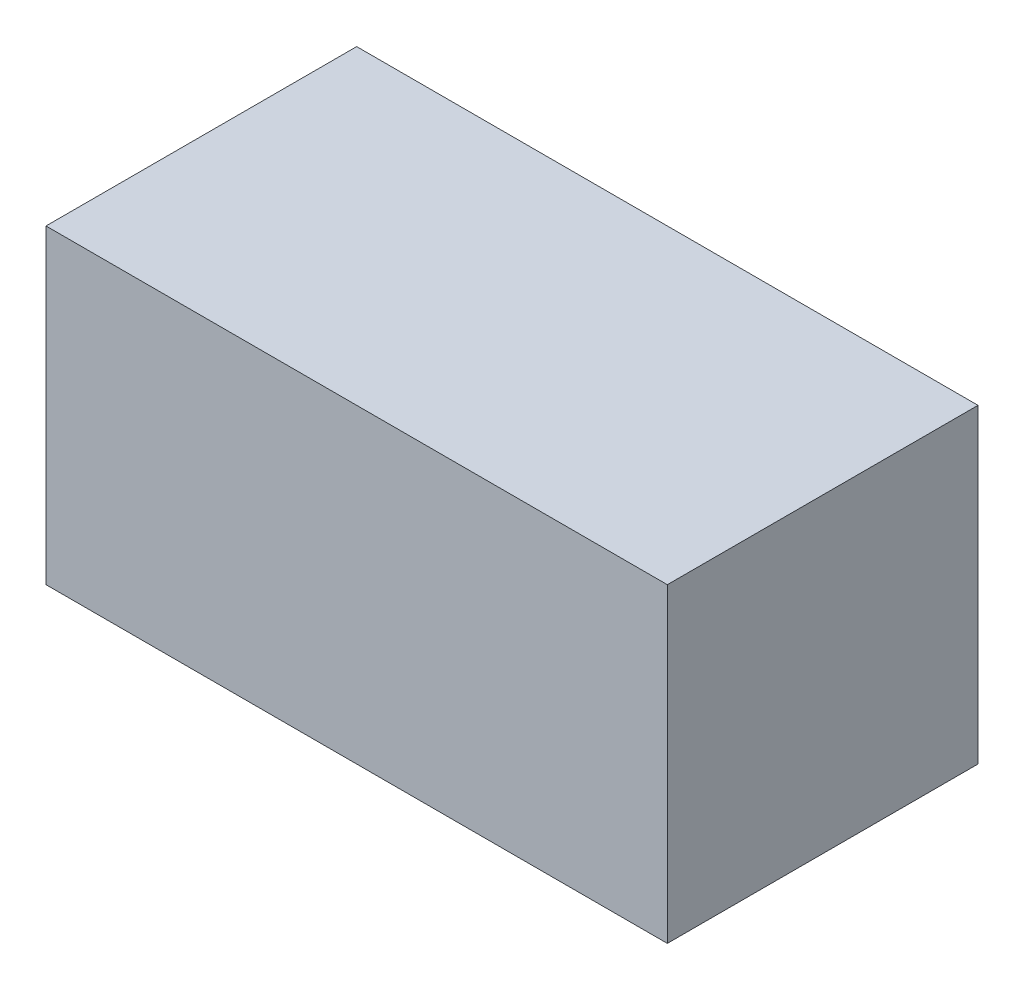
SolidWorks part; units mm, degrees
ref_plane "Front" through (0, 0, 0) normal (0, 0, 1) x (1, 0, 0)
ref_plane "Top" through (0, 0, 0) normal (0, 1, 0) x (1, 0, 0)
ref_plane "Right" through (0, 0, 0) normal (1, 0, 0) x (0, 0, -1)
sketch "Sketch1" plane through (0, 0, 0) normal (0, 1, 0) x (1, 0, 0)
  line L1 (0, 0) -> (20, 0)
  line L2 (0, 0) -> (0, 10)
  line L3 (0, 10) -> (20, 10)
  line L4 (20, 0) -> (20, 10)
  dimension "D1" = 10
  dimension "D2" = 20
extrude "Extrude1" add sketch "Sketch1" along normal blind 10
